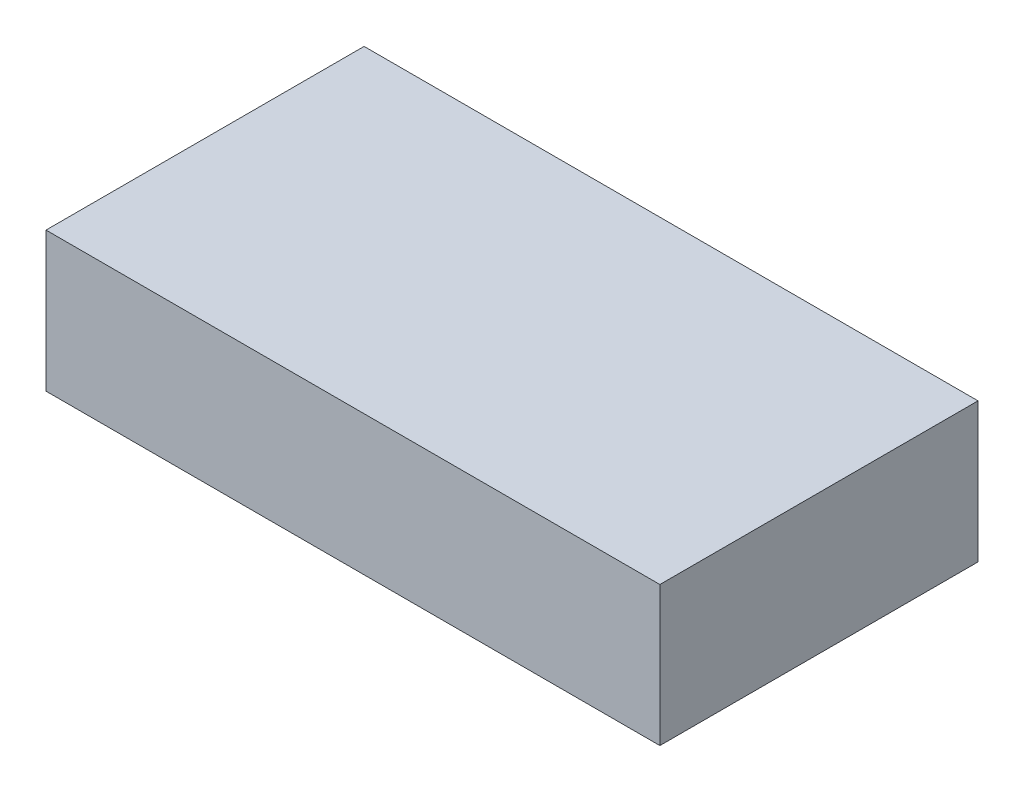
SolidWorks part; units mm, degrees
ref_plane "Front Plane" through (0, 0, 0) normal (0, 0, 1) x (1, 0, 0)
ref_plane "Top Plane" through (0, 0, 0) normal (0, 1, 0) x (1, 0, 0)
ref_plane "Right Plane" through (0, 0, 0) normal (1, 0, 0) x (0, 0, -1)
sketch "Sketch1" plane through (0, 0, 0) normal (0, 1, 0) x (1, 0, 0)
  line L1 (-110, 57) -> (110, 57)
  line L2 (-110, 57) -> (-110, -57)
  line L3 (-110, -57) -> (110, -57)
  line L4 (110, 57) -> (110, -57)
  line L5 (-110, 57) -> (110, -57) construction
  line L6 (-110, -57) -> (110, 57) construction
  point P0 (0, 0)
  dimension "D1" = 114
  dimension "D2" = 220
extrude "Boss-Extrude1" add sketch "Sketch1" along normal blind 50
